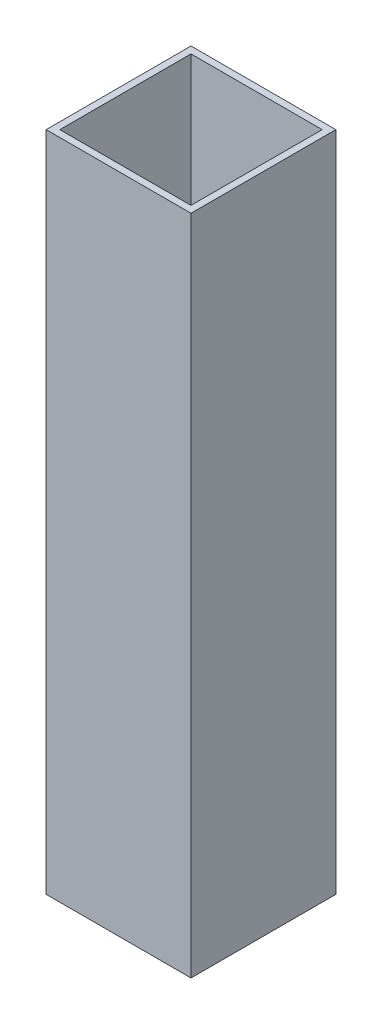
SolidWorks part; units mm, degrees
ref_plane "Alzado" through (0, 0, 0) normal (0, 0, 1) x (1, 0, 0)
ref_plane "Planta" through (0, 0, 0) normal (0, 1, 0) x (1, 0, 0)
ref_plane "Vista lateral" through (0, 0, 0) normal (1, 0, 0) x (0, 0, -1)
sketch "Sketch1" plane through (0, 0, 0) normal (0, 1, 0) x (1, 0, 0)
  line L0 (0, 0) -> (25.4, 0)
  line L1 (25.4, 0) -> (25.4, 25.4)
  line L2 (25.4, 25.4) -> (0, 25.4)
  line L3 (0, 25.4) -> (0, 0)
  line L4 (1.2, 24.2) -> (1.2, 1.2)
  line L5 (1.2, 1.2) -> (24.2, 1.2)
  line L6 (24.2, 1.2) -> (24.2, 24.2)
  line L7 (24.2, 24.2) -> (1.2, 24.2)
  dimension "D1" = 25.4
  dimension "D2" = 25.4
  dimension "D3" = 1.2
  dimension "D4" = 1.2
  dimension "D5" = 1.2
  dimension "D6" = 1.2
extrude "Boss-Extrude1" add sketch "Sketch1" along normal blind 116.13
